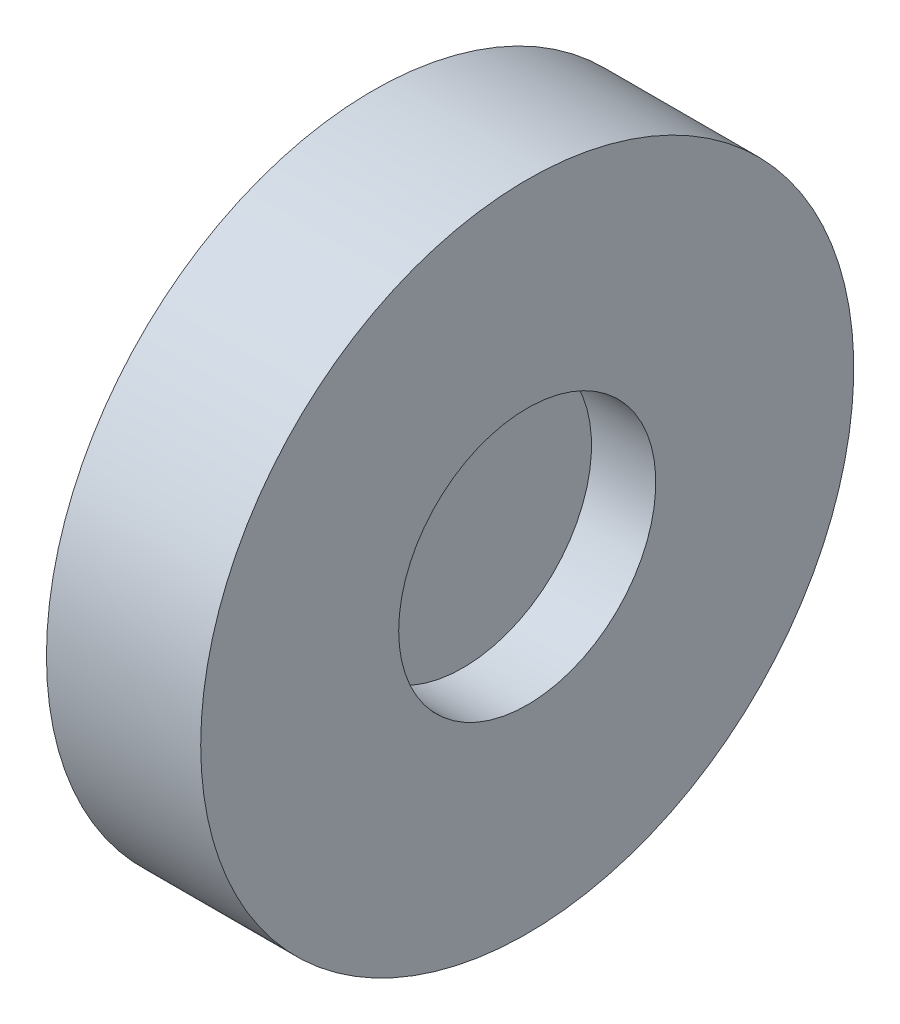
SolidWorks part; units mm, degrees
ref_plane "前视基准面" through (0, 0, 0) normal (0, 0, 1) x (1, 0, 0)
ref_plane "上视基准面" through (0, 0, 0) normal (0, 1, 0) x (1, 0, 0)
ref_plane "右视基准面" through (0, 0, 0) normal (1, 0, 0) x (0, 0, -1)
sketch "草图1" plane through (0, 0, 0) normal (0, 0, 1) x (1, 0, 0)
  line L0 (-0.5, 5) -> (-0.5, 0)
  line L2 (-0.5, 5) -> (0.5, 5)
  line L3 (-0.5, 0) -> (0.5, 0)
  line L4 (0.5, 5) -> (0.5, 0)
revolve "旋转2" add sketch "草图1" angle 360 about L3
sketch "草图4" plane through (0, 0, 0) normal (0, 0, 1) x (1, 0, 0)
  line L0 (-3, 12.7) -> (3, 12.7)
  line L1 (3, 12.7) -> (3, 5)
  line L2 (3, 5) -> (-3, 5)
  line L3 (0.5, 5) -> (-0.5, 5) construction
  line L4 (-3, 5) -> (-3, 12.7)
  line L5 (0, 5) -> (0, 12.7) construction
  line L6 (-1.6142, 0) -> (1.5903, 0) construction
revolve "旋转3" add sketch "草图4" angle 360 about L6
equation "\"D1@草图4\"=\"D1@草图1\""
